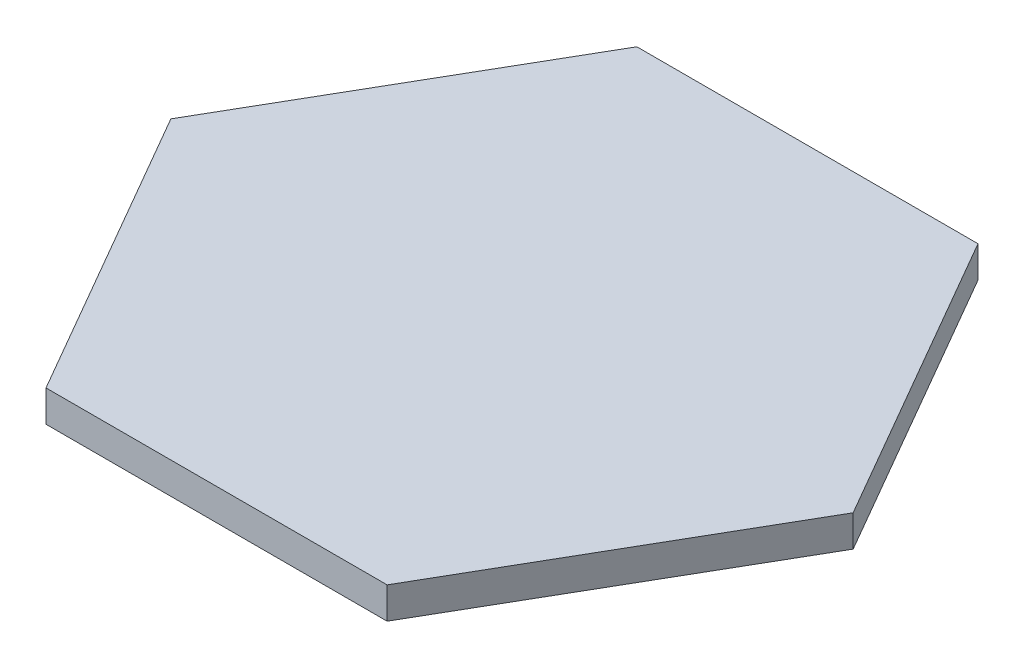
SolidWorks part; units mm, degrees
ref_plane "Alzado" through (0, 0, 0) normal (0, 0, 1) x (1, 0, 0)
ref_plane "Planta" through (0, 0, 0) normal (0, 1, 0) x (1, 0, 0)
ref_plane "Vista lateral" through (0, 0, 0) normal (1, 0, 0) x (0, 0, -1)
sketch "Croquis1" plane through (0, 0, 0) normal (0, 1, 0) x (1, 0, 0)
  line L1 (-32.5, 0) -> (-16.25, -28.1458)
  line L2 (-16.25, -28.1458) -> (16.25, -28.1458)
  line L3 (16.25, -28.1458) -> (32.5, 0)
  line L4 (32.5, 0) -> (16.25, 28.1458)
  line L5 (16.25, 28.1458) -> (-16.25, 28.1458)
  line L6 (-16.25, 28.1458) -> (-32.5, 0)
  circle A0 centre (0, 0) radius 28.1458 construction
  point P1 (30, 0)
  point P10 (-29.9249, 2.1215)
  point P11 (-30, 0)
  dimension "D1" = 65
extrude "Saliente-Extruir1" add sketch "Croquis1" along normal blind 3
